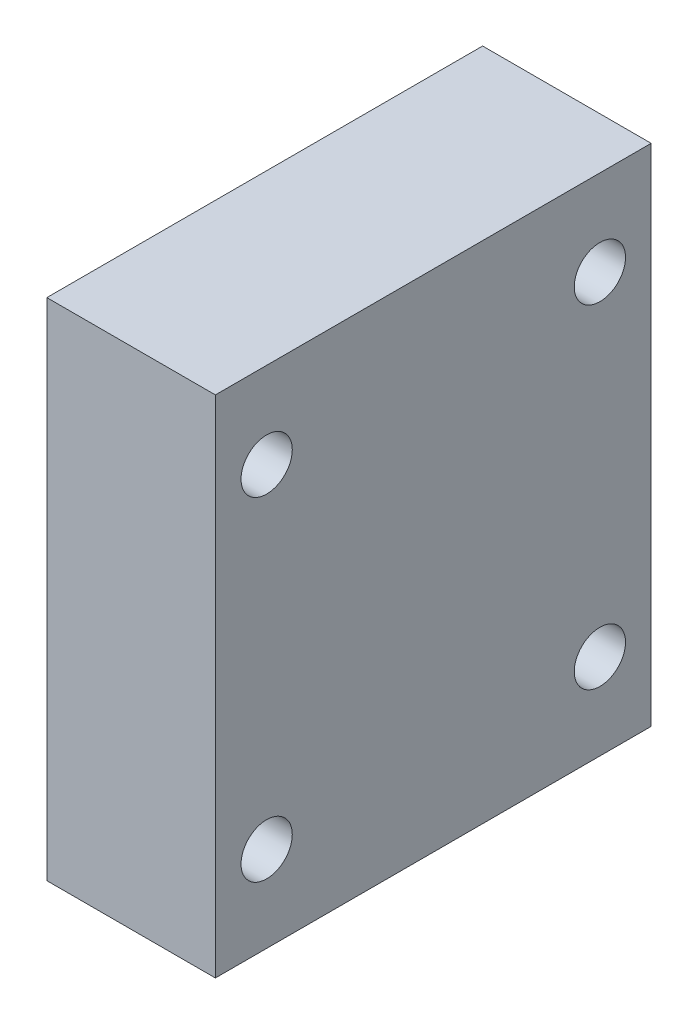
SolidWorks part; units mm, degrees
ref_plane "Спереди" through (0, 0, 0) normal (0, 0, 1) x (1, 0, 0)
ref_plane "Сверху" through (0, 0, 0) normal (0, 1, 0) x (1, 0, 0)
ref_plane "Справа" through (0, 0, 0) normal (1, 0, 0) x (0, 0, -1)
sketch "Эскиз1" plane through (0, 0, 0) normal (1, 0, 0) x (0, 0, -1)
  line L1 (-17, -19.7) -> (17, -19.7)
  line L2 (-17, -19.7) -> (-17, 19.7)
  line L3 (-17, 19.7) -> (17, 19.7)
  line L4 (17, -19.7) -> (17, 19.7)
  line L5 (-17, -19.7) -> (17, 19.7) construction
  line L6 (-17, 19.7) -> (17, -19.7) construction
  line L7 (-13, -13) -> (13, -13) construction
  line L8 (-13, -13) -> (-13, 13) construction
  line L9 (-13, 13) -> (13, 13) construction
  line L10 (13, -13) -> (13, 13) construction
  line L11 (-13, -13) -> (13, 13) construction
  line L12 (-13, 13) -> (13, -13) construction
  circle A0 centre (-13, 13) radius 2
  circle A1 centre (13, 13) radius 2
  circle A2 centre (13, -13) radius 2
  circle A3 centre (-13, -13) radius 2
  point P0 (0, 0)
  point P5 (0, 0)
  dimension "D4" = 4
  dimension "D5" = 4
  dimension "D6" = 4
  dimension "D7" = 4
  dimension "D1" = 39.4
  dimension "D2" = 34
  dimension "D3" = 26
extrude "Бобышка-Вытянуть1" add sketch "Эскиз1" along normal blind 13.15
